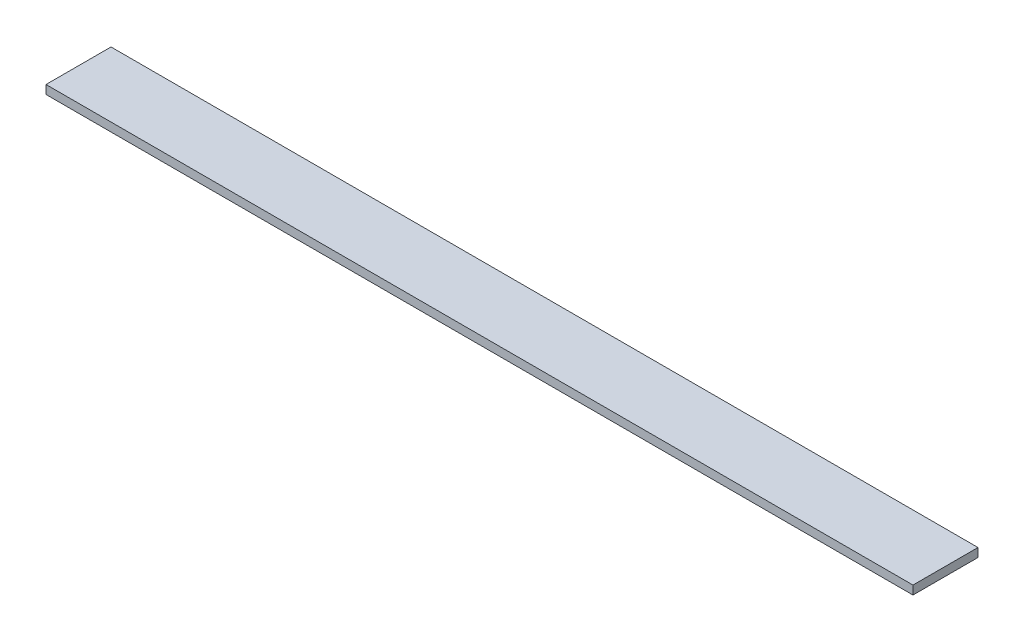
SolidWorks part; units mm, degrees
ref_plane "Спереди" through (0, 0, 0) normal (0, 0, 1) x (1, 0, 0)
ref_plane "Сверху" through (0, 0, 0) normal (0, 1, 0) x (1, 0, 0)
ref_plane "Справа" through (0, 0, 0) normal (1, 0, 0) x (0, 0, -1)
sketch "Эскиз1" plane through (0, 0, 0) normal (1, 0, 0) x (0, 0, -1)
  line L1 (-15, -2) -> (15, -2)
  line L2 (-15, -2) -> (-15, 2)
  line L3 (-15, 2) -> (15, 2)
  line L4 (15, -2) -> (15, 2)
  line L5 (-15, -2) -> (15, 2) construction
  line L6 (-15, 2) -> (15, -2) construction
  point P0 (0, 0)
  dimension "D1" = 4
  dimension "D2" = 30
extrude "Бобышка-Вытянуть1" add sketch "Эскиз1" along normal blind 400
